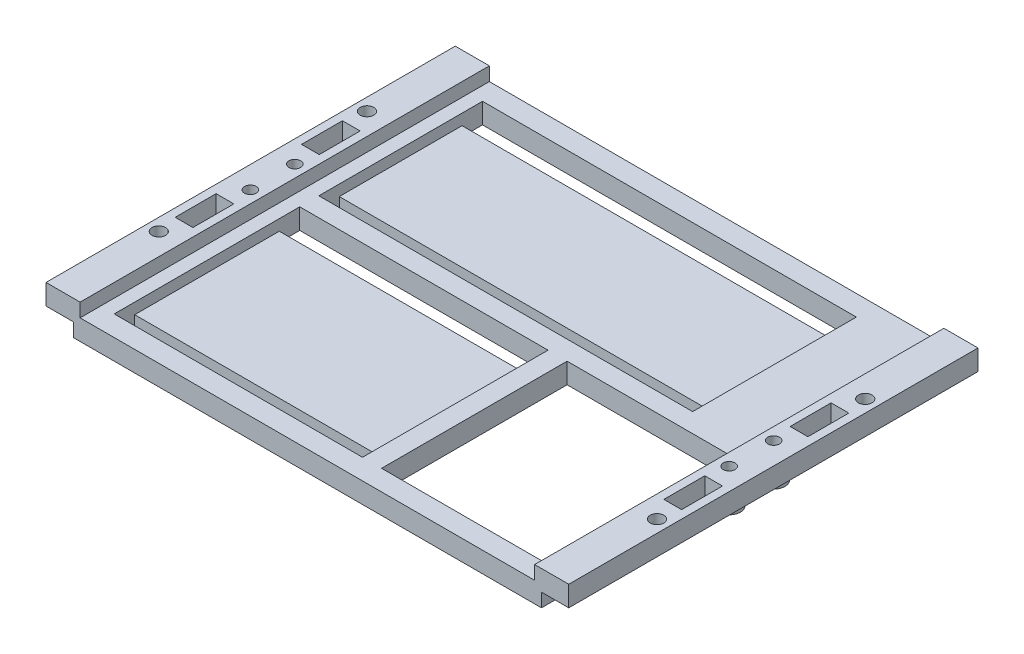
SolidWorks part; units mm, degrees
material "PET"
ref_plane "Front Plane" through (0, 0, 0) normal (0, 0, 1) x (1, 0, 0)
ref_plane "Top Plane" through (0, 0, 0) normal (0, 1, 0) x (1, 0, 0)
ref_plane "Right Plane" through (0, 0, 0) normal (1, 0, 0) x (0, 0, -1)
sketch "Sketch2" plane through (0, 0, 0) normal (0, 0, 1) x (1, 0, 0)
  line L0 (179.1, 12.5) -> (191.6, 12.5)
  line L1 (7.5, 0) -> (184.1, 0)
  line L2 (0, 5) -> (0, 12.5)
  line L3 (0, 12.5) -> (12.5, 12.5)
  line L4 (191.6, 5) -> (191.6, 12.5)
  line L7 (0, 5) -> (7.5, 5)
  line L8 (7.5, 0) -> (7.5, 5)
  line L11 (191.6, 5) -> (184.1, 5)
  line L12 (184.1, 0) -> (184.1, 5)
  line L14 (12.5, 12.5) -> (12.5, 7.5)
  line L15 (12.5, 7.5) -> (179.1, 7.5)
  line L16 (179.1, 12.5) -> (179.1, 7.5)
  dimension "D1" = 191.6
  dimension "D2" = 5
  dimension "D3" = 5
  dimension "D4" = 5
  dimension "D5" = 12.5
  dimension "D6" = 7.5
  dimension "D7" = 7.5
  dimension "D8" = 12.5
  dimension "D9" = 12.5
extrude "PlateFrame" add sketch "Sketch2" along normal blind 150
sketch "Sketch3" plane through (0, 12.5, 0) normal (0, 1, 0) x (1, 0, 0)
  line L0 (12.5, 0) -> (0, 0) construction
  line L2 (0, -150) -> (0, 0) construction
  line L3 (191.6, -150) -> (191.6, 0) construction
  line L4 (191.6, 0) -> (179.1, 0) construction
  circle A0 centre (8.05, -66.85) radius 2.5
  circle A1 centre (8.05, -83.15) radius 2.5
  circle A2 centre (183.55, -66.85) radius 2.5
  circle A3 centre (183.55, -83.15) radius 2.5
  dimension "D1" = 5
  dimension "D2" = 5
  dimension "D3" = 5
  dimension "D4" = 5
  dimension "D5" = 66.85
  dimension "D6" = 16.3
  dimension "D7" = 8.05
  dimension "D8" = 8.05
  dimension "D9" = 8.05
  dimension "D10" = 8.05
  dimension "D11" = 66.85
  dimension "D12" = 16.3
  dimension "D13" = 175.5
extrude "HoleSupport" cut sketch "Sketch3" against normal through all
sketch "Sketch4" plane through (0, 12.5, 0) normal (0, 1, 0) x (1, 0, 0)
  circle A0 centre (8.05, -66.85) radius 2.15
  circle A1 centre (8.05, -83.15) radius 2.15
  circle A2 centre (183.55, -83.15) radius 2.15
  circle A3 centre (183.55, -66.85) radius 2.15
  circle A4 centre (183.55, -66.85) radius 4.15
  circle A5 centre (183.55, -83.15) radius 4.15
  circle A6 centre (8.05, -66.85) radius 4.15
  circle A7 centre (8.05, -83.15) radius 4.15
  dimension "D1" = 2
extrude "CylindricalSupports" add sketch "Sketch4" against normal blind 12.5
sketch "Sketch8" plane through (0, 7.5, 0) normal (0, 1, 0) x (1, 0, 0)
  line L0 (12.5, -150) -> (12.5, 0) construction
  line L2 (154.5, -7.5) -> (17.5, -7.5)
  line L3 (154.5, -7.5) -> (154.5, -67.5)
  line L4 (154.5, -67.5) -> (17.5, -67.5)
  line L5 (17.5, -7.5) -> (17.5, -67.5)
  line L6 (108.5, -142.5) -> (17.5, -142.5)
  line L7 (108.5, -142.5) -> (108.5, -74.5)
  line L8 (108.5, -74.5) -> (17.5, -74.5)
  line L9 (17.5, -142.5) -> (17.5, -74.5)
  line L10 (179.1, 0) -> (12.5, 0) construction
  line L11 (179.1, -150) -> (12.5, -150) construction
  dimension "D1" = 5
  dimension "D2" = 7.5
  dimension "D3" = 7.5
  dimension "D4" = 5
  dimension "D5" = 60
  dimension "D6" = 68
  dimension "D7" = 137
  dimension "D8" = 91
extrude "ItemLayout" cut sketch "Sketch8" against normal blind 4
sketch "Sketch9" plane through (0, 7.5, 0) normal (0, 1, 0) x (1, 0, 0)
  line L0 (179.1, -150) -> (179.1, 0) construction
  line L1 (115.5, -74.5) -> (174.1, -74.5)
  line L2 (115.5, -74.5) -> (115.5, -142.5)
  line L3 (115.5, -142.5) -> (174.1, -142.5)
  line L4 (174.1, -74.5) -> (174.1, -142.5)
  line L5 (179.1, -150) -> (12.5, -150) construction
  line L7 (108.5, -142.5) -> (108.5, -74.5) construction
  dimension "D1" = 5
  dimension "D2" = 7.5
  dimension "D3" = 68
  dimension "D4" = 7
extrude "HoleCutout" cut sketch "Sketch9" against normal blind 7.5
sketch "Sketch10" plane through (0, 3.5, 0) normal (0, 1, 0) x (1, 0, 0)
  line L0 (108.5, -142.5) -> (108.5, -74.5) construction
  line L1 (17.5, -74.5) -> (108.5, -74.5)
  line L2 (17.5, -74.5) -> (17.5, -82)
  line L3 (17.5, -82) -> (108.5, -82)
  line L4 (108.5, -74.5) -> (108.5, -82)
  line L5 (108.5, -142.5) -> (108.5, -74.5) construction
  line L6 (17.5, -142.5) -> (108.5, -142.5)
  line L7 (17.5, -142.5) -> (17.5, -135)
  line L8 (17.5, -135) -> (108.5, -135)
  line L9 (108.5, -142.5) -> (108.5, -135)
  line L10 (154.5, -67.5) -> (154.5, -7.5) construction
  line L11 (17.5, -7.5) -> (154.5, -7.5)
  line L12 (17.5, -7.5) -> (17.5, -15)
  line L13 (17.5, -15) -> (154.5, -15)
  line L14 (154.5, -7.5) -> (154.5, -15)
  line L16 (17.5, -67.5) -> (154.5, -67.5)
  line L17 (17.5, -67.5) -> (17.5, -60)
  line L18 (17.5, -60) -> (154.5, -60)
  line L19 (154.5, -67.5) -> (154.5, -60)
  dimension "D1" = 7.5
  dimension "D2" = 7.5
  dimension "D3" = 7.5
  dimension "D4" = 7.5
extrude "VelcroCut" cut sketch "Sketch10" against normal blind 3.5
sketch "Sketch11" plane through (0, 12.5, 0) normal (0, 1, 0) x (1, 0, 0)
  line L0 (12.5, -150) -> (12.5, 0) construction
  line L1 (9.5, -59.35) -> (3, -59.35)
  line L2 (9.5, -59.35) -> (9.5, -44.35)
  line L3 (9.5, -44.35) -> (3, -44.35)
  line L4 (3, -59.35) -> (3, -44.35)
  line L5 (188.6, -59.35) -> (182.1, -59.35)
  line L6 (188.6, -59.35) -> (188.6, -44.35)
  line L7 (188.6, -44.35) -> (182.1, -44.35)
  line L8 (182.1, -59.35) -> (182.1, -44.35)
  line L9 (182.1, -90.65) -> (188.6, -90.65)
  line L10 (182.1, -90.65) -> (182.1, -105.65)
  line L11 (182.1, -105.65) -> (188.6, -105.65)
  line L12 (188.6, -90.65) -> (188.6, -105.65)
  line L13 (3, -90.65) -> (9.5, -90.65)
  line L14 (3, -90.65) -> (3, -105.65)
  line L15 (3, -105.65) -> (9.5, -105.65)
  line L16 (9.5, -90.65) -> (9.5, -105.65)
  line L17 (12.5, -150) -> (12.5, 0) construction
  line L18 (179.1, -150) -> (179.1, 0) construction
  line L19 (179.1, -150) -> (179.1, 0) construction
  circle A4 centre (8.05, -66.85) radius 2.15 construction
  circle A5 centre (8.05, -83.15) radius 2.15 construction
  circle A6 centre (183.55, -66.85) radius 2.15 construction
  circle A7 centre (183.55, -83.15) radius 2.15 construction
  dimension "D2" = 7.5
  dimension "D12" = 7.5
  dimension "D11" = 7.5
  dimension "D17" = 7.5
  dimension "D3" = 3
  dimension "D4" = 3
  dimension "D5" = 6.5
  dimension "D6" = 15
  dimension "D7" = 6.5
  dimension "D8" = 15
  dimension "D9" = 3
  dimension "D10" = 3
  dimension "D13" = 15
  dimension "D14" = 15
  dimension "D15" = 6.5
  dimension "D16" = 6.5
extrude "CutShellHoles" cut sketch "Sketch11" against normal blind 12.5
sketch "Sketch12" plane through (0, 12.5, 0) normal (0, 1, 0) x (1, 0, 0)
  line L0 (12.5, -150) -> (12.5, 0) construction
  line L1 (12.5, -150) -> (12.5, 0) construction
  line L2 (179.1, -150) -> (179.1, 0) construction
  line L3 (179.1, -150) -> (179.1, 0) construction
  circle A0 centre (4.5, -36.85) radius 2.5
  circle A1 centre (4.5, -113.15) radius 2.5
  circle A2 centre (187.1, -36.85) radius 2.5
  circle A3 centre (187.1, -113.15) radius 2.5
  circle A4 centre (8.05, -66.85) radius 2.15 construction
  circle A5 centre (8.05, -83.15) radius 2.15 construction
  circle A6 centre (183.55, -66.85) radius 2.15 construction
  circle A7 centre (183.55, -83.15) radius 2.15 construction
  dimension "D1" = 30
  dimension "D2" = 30
  dimension "D3" = 30
  dimension "D4" = 30
  dimension "D5" = 8
  dimension "D6" = 5
  dimension "D7" = 5
  dimension "D8" = 8
  dimension "D9" = 5
  dimension "D10" = 5
  dimension "D11" = 8
  dimension "D12" = 8
extrude "StandoffHoles" cut sketch "Sketch12" against normal through all
sketch "Sketch13" plane through (0, 0, 0) normal (0, -1, 0) x (1, 0, 0)
  line L0 (7.5, 150) -> (184.1, 150) construction
  line L1 (7.5, 0) -> (10, 0)
  line L2 (7.5, 0) -> (7.5, 41)
  line L3 (7.5, 41) -> (10, 41)
  line L4 (10, 0) -> (10, 41)
  line L5 (7.5, 150) -> (10, 150)
  line L6 (7.5, 150) -> (7.5, 109)
  line L7 (7.5, 109) -> (10, 109)
  line L8 (10, 150) -> (10, 109)
  line L9 (181.6, 150) -> (184.1, 150)
  line L10 (181.6, 150) -> (181.6, 109)
  line L11 (181.6, 109) -> (184.1, 109)
  line L12 (184.1, 150) -> (184.1, 109)
  line L13 (184.1, 150) -> (184.1, 105.65) construction
  line L14 (7.5, 0) -> (184.1, 0) construction
  line L15 (181.6, 0) -> (184.1, 0)
  line L16 (181.6, 0) -> (181.6, 41)
  line L17 (181.6, 41) -> (184.1, 41)
  line L18 (184.1, 0) -> (184.1, 41)
  line L19 (184.1, 44.35) -> (184.1, 0) construction
  dimension "D1" = 41
  dimension "D2" = 41
  dimension "D3" = 41
  dimension "D4" = 41
  dimension "D5" = 2.5
  dimension "D6" = 2.5
  dimension "D7" = 2.5
  dimension "D8" = 2.5
extrude "CutStandoffRoom" cut sketch "Sketch13" against normal blind 5
